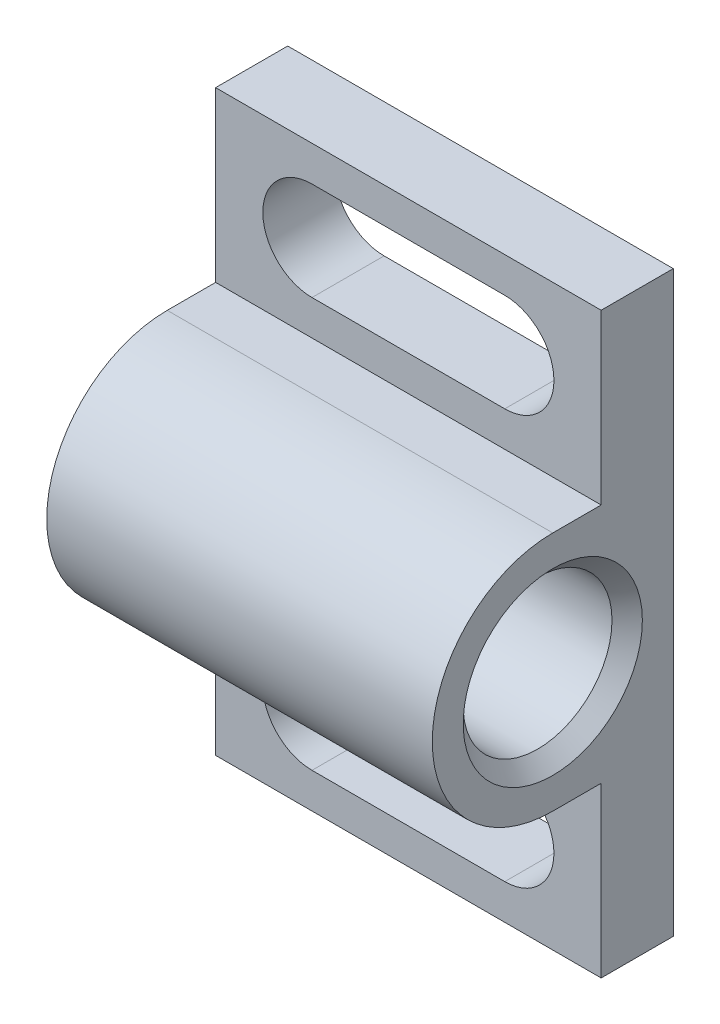
SolidWorks part; units mm, degrees
ref_plane "Front Plane" through (0, 0, 0) normal (0, 0, 1) x (1, 0, 0)
ref_plane "Top Plane" through (0, 0, 0) normal (0, 1, 0) x (1, 0, 0)
ref_plane "Right Plane" through (0, 0, 0) normal (1, 0, 0) x (0, 0, -1)
sketch "Sketch1" plane through (0, 0, 0) normal (1, 0, 0) x (0, 0, -1)
  line L0 (0, -19.05) -> (0, 19.05)
  line L3 (-4.7498, -19.05) -> (-4.7498, -7.9375)
  line L4 (-4.7498, 19.05) -> (0, 19.05)
  line L5 (0, -19.05) -> (-4.7498, -19.05)
  line L16 (-4.7498, 7.9375) -> (-4.7498, 19.05)
  line L17 (0, 0) -> (-15.875, 0) construction
  line L18 (-7.9375, 7.9375) -> (-4.7498, 7.9375)
  line L19 (-7.9375, -7.9375) -> (-4.7498, -7.9375)
  arc A10 (-7.9375, 7.9375) -> (-7.9375, -7.9375) centre (-7.9375, 0) ccw
  circle A12 centre (-7.9375, 0) radius 7.9375 construction
  dimension "D1" = 38.1
  dimension "D2" = 15.875
  dimension "D3" = 4.7498
extrude "Boss-Extrude1" add sketch "Sketch1" against normal blind 25.4
sketch "Sketch2" plane through (0, 0, 0) normal (0, 1, 0) x (1, 0, 0)
  line L0 (0, -7.9375) -> (-25.4, -7.9375) construction
  line L1 (-25.4, -7.9375) -> (-25.4, -15.875) construction
  line L2 (-25.4, -7.9375) -> (-25.4, -10.4902)
  line L3 (-25.4, -10.4902) -> (-19.05, -10.4902)
  line L4 (-19.05, -10.4902) -> (-19.05, -12.8397)
  line L5 (-19.05, -12.8397) -> (-1, -12.8397)
  line L6 (-1, -12.8397) -> (0, -13.8397)
  line L7 (0, -13.8397) -> (0, -7.9375)
  line L8 (0, -7.9375) -> (-25.4, -7.9375)
  dimension "D1" = 5.1054
  dimension "D2" = 9.8044
  dimension "D3" = 19.05
  dimension "D4" = 1
  dimension "D5" = 45
revolve "Cut-Revolve1" cut sketch "Sketch2" angle 360 mid plane about L0
sketch "Sketch3" plane through (0, 0, 0) normal (0, 0, 1) x (1, 0, 0)
  line L0 (-19.05, 13.4874) -> (-6.35, 13.4874) construction
  line L1 (-19.05, 16.7259) -> (-6.35, 16.7259)
  line L2 (-19.05, 10.2489) -> (-6.35, 10.2489)
  line L3 (-25.4, 0) -> (0, 0) construction
  line L4 (-25.4, -19.05) -> (-25.4, 19.05) construction
  line L5 (-19.05, -13.4874) -> (-6.35, -13.4874) construction
  line L6 (-19.05, -16.7259) -> (-6.35, -16.7259)
  line L7 (-19.05, -10.2489) -> (-6.35, -10.2489)
  line L8 (-12.7, 13.4874) -> (-12.7, 0) construction
  arc A0 (-19.05, 16.7259) -> (-19.05, 10.2489) centre (-19.05, 13.4874) ccw
  arc A1 (-6.35, 10.2489) -> (-6.35, 16.7259) centre (-6.35, 13.4874) ccw
  arc A2 (-19.05, -16.7259) -> (-19.05, -10.2489) centre (-19.05, -13.4874) cw
  arc A3 (-6.35, -10.2489) -> (-6.35, -16.7259) centre (-6.35, -13.4874) cw
  point P2 (-12.7, 13.4874)
  point P14 (-12.7, -13.4874)
  dimension "D1" = 26.9748
  dimension "D2" = 6.477
  dimension "D3" = 12.7
extrude "Cut-Extrude2" cut sketch "Sketch3" along normal up to next
